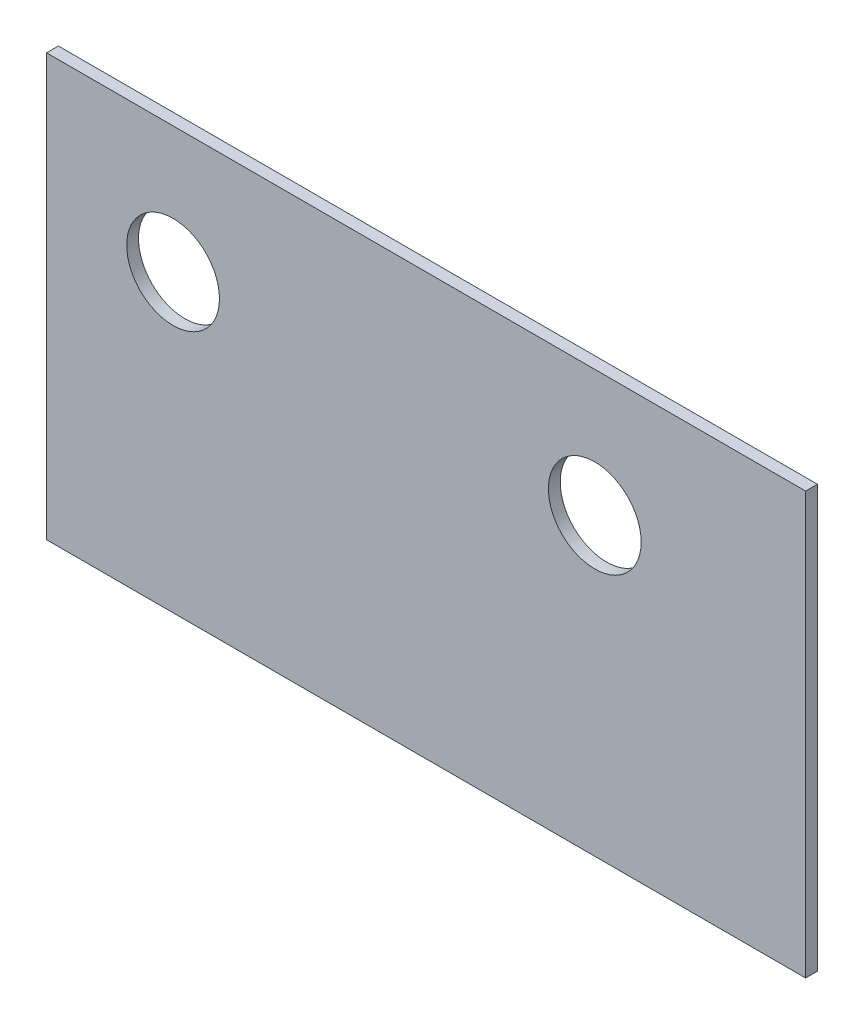
SolidWorks part; units mm, degrees
ref_plane "Front Plane" through (0, 0, 0) normal (0, 0, 1) x (1, 0, 0)
ref_plane "Top Plane" through (0, 0, 0) normal (0, 1, 0) x (1, 0, 0)
ref_plane "Right Plane" through (0, 0, 0) normal (1, 0, 0) x (0, 0, -1)
sketch "Sketch1" plane through (0, 0, 0) normal (0, 0, 1) x (1, 0, 0)
  line L1 (180, 100) -> (0, 100)
  line L2 (180, 100) -> (180, 0)
  line L3 (180, 0) -> (0, 0)
  line L4 (0, 100) -> (0, 0)
  circle A0 centre (30, 70) radius 11
  circle A3 centre (130, 70) radius 11
  point P6 (-52.648, 5.8309)
  point P9 (65.1205, 10.227)
  point P10 (0, 0)
  dimension "D2" = 30
  dimension "D3" = 30
  dimension "D5" = 30
  dimension "D7" = 22
  dimension "D8" = 22
  dimension "D1" = 100
  dimension "D4" = 100
  dimension "D6" = 180
extrude "Boss-Extrude1" add sketch "Sketch1" along normal blind 2.8
